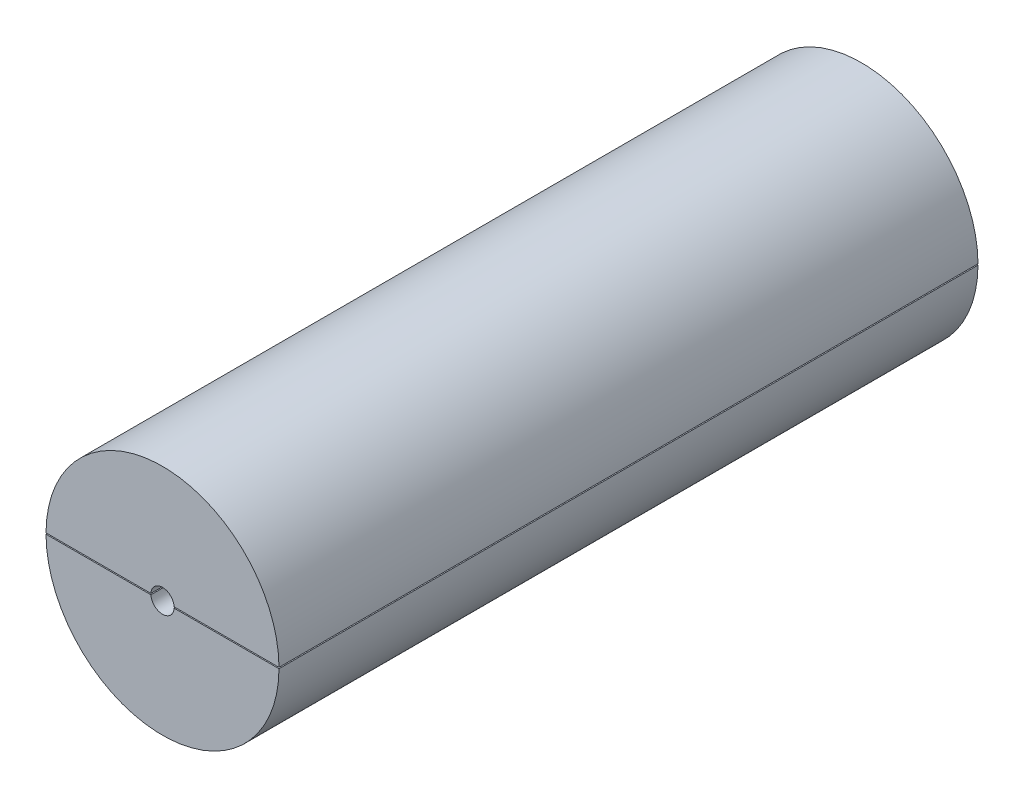
SolidWorks part; units mm, degrees
ref_plane "Plan de face" through (0, 0, 0) normal (0, 0, 1) x (1, 0, 0)
ref_plane "Plan de dessus" through (0, 0, 0) normal (0, 1, 0) x (1, 0, 0)
ref_plane "Plan de droite" through (0, 0, 0) normal (1, 0, 0) x (0, 0, -1)
sketch "Esquisse1" plane through (0, 0, 0) normal (0, 0, 1) x (1, 0, 0)
  circle A0 centre (0, 0) radius 20
extrude "Boss.-Extru.1" add sketch "Esquisse1" against normal blind 120
ref_plane "Plan1" through (0, 0, -5) normal (0, 0, 1) x (1, 0, 0)
sketch "Esquisse3" plane through (0, 0, -5) normal (0, 0, 1) x (1, 0, 0)
  circle A0 centre (0, 0) radius 16
extrude "Enlèv. mat.-Extru.1" cut sketch "Esquisse3" against normal blind 90
ref_plane "Plan3" through (0, 0, 0) normal (0, 1, 0) x (1, 0, 0)
sketch "Esquisse6" plane through (0, 0, -120) normal (0, 0, -1) x (-1, 0, 0)
  line L0 (-21.4279, 0) -> (-21.4279, -0.1)
  line L1 (21.9997, 0) -> (-21.9997, 0) construction
  line L2 (-21.4279, -0.1) -> (22.2825, -0.1)
  line L3 (22.2825, -0.1) -> (22.2825, 0.1)
  line L4 (22.2825, 0.1) -> (-21.4279, 0.1)
  line L5 (-21.4279, 0.1) -> (-21.4279, 0)
extrude "Enlèv. mat.-Extru.3" cut sketch "Esquisse6" against normal blind 130
sketch "Esquisse7" plane through (0, -0.1, 0) normal (0, 1, 0) x (1, 0, 0)
  line L2 (-15.9997, 95) -> (15.9997, 95)
  arc A1 (-15.9997, 95) -> (15.9997, 95) centre (0, 95) cw
revolve "Enlèvement de matière-Révolution2" cut sketch "Esquisse7" angle 360 about L2
sketch "Esquisse8" plane through (0, 0.1, 0) normal (0, -1, 0) x (1, 0, 0)
  line L0 (-15.9997, -95) -> (15.9997, -95)
  line L1 (15.9997, -95) -> (-15.9997, -95) construction
  arc A0 (-15.9997, -95) -> (15.9997, -95) centre (0, -95) cw
  point P3 (0, -95)
revolve "Enlèvement de matière-Révolution3" cut sketch "Esquisse8" angle 360 about L0
sketch "Esquisse9" plane through (0, 0, 0) normal (0, 0, 1) x (1, 0, 0)
  circle A0 centre (0, 0) radius 2
extrude "Enlèv. mat.-Extru.4" cut sketch "Esquisse9" against normal blind 10
